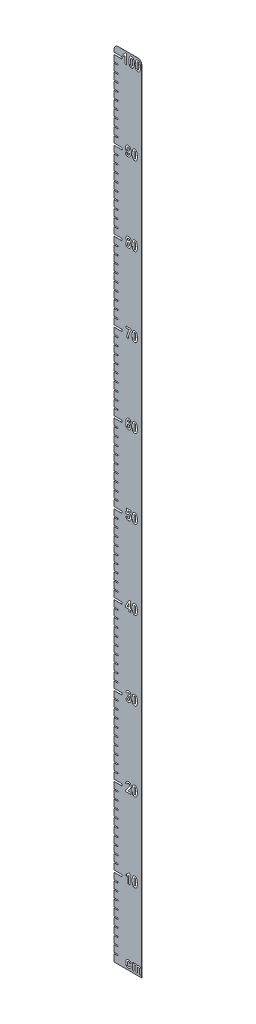
SolidWorks part; units mm, degrees
ref_plane "Plano frontal" through (0, 0, 0) normal (0, 0, 1) x (1, 0, 0)
ref_plane "Plano superior" through (0, 0, 0) normal (0, 1, 0) x (1, 0, 0)
ref_plane "Plano direito" through (0, 0, 0) normal (1, 0, 0) x (0, 0, -1)
sketch "Esboço1" plane through (0, 0, 0) normal (0, 0, 1) x (1, 0, 0)
  line L1 (0, 0) -> (35, 0)
  line L2 (0, 0) -> (0, 1010)
  line L3 (0, 1010) -> (35, 1010)
  line L4 (35, 0) -> (35, 1010)
  dimension "D1" = 1010
  dimension "D2" = 35
extrude "Ressalto-extrusão1" add sketch "Esboço1" along normal blind 0.1
sketch "Esboço2" plane through (0, 0, 0.1) normal (0, 0, 1) x (1, 0, 0)
  line L0 (0, 10) -> (5, 10)
  line L1 (0, 1010) -> (0, 0) construction
  line L2 (0, 0) -> (35, 0) construction
  dimension "D1" = 5
  dimension "D2" = 10
extrude "Corte-Extrusão-Fina1" cut sketch "Esboço2" against normal blind 1 and the other way through all thin thin type mid plane wall 1.5
pattern_linear "Padrão linear1" count 9 spacing 10 along (0, 1, 0) of "Corte-Extrusão-Fina1"
sketch "Esboço3" plane through (0, 0, 0.1) normal (0, 0, 1) x (1, 0, 0)
  line L0 (0, 100) -> (10, 100)
  line L1 (0, 1010) -> (0, 90.75) construction
  line L2 (0, 0) -> (35, 0) construction
  dimension "D1" = 10
  dimension "D2" = 100
extrude "Corte-Extrusão-Fina2" cut sketch "Esboço3" against normal blind 1 and the other way through all thin thin type mid plane wall 2.5
pattern_linear "Padrão linear2" count 2 spacing 100 along (0, 1, 0) of "Corte-Extrusão-Fina2"
pattern_linear "Padrão linear3" count 10 spacing 100 along (0, 1, 0) of "Corte-Extrusão-Fina1", "Padrão linear1", "Corte-Extrusão-Fina2"
sketch "Esboço5" plane through (0, 0, 0.1) normal (0, 0, 1) x (1, 0, 0)
  line L0 (10, 95) -> (40, 95) construction
  line L2 (10, 101.25) -> (10, 98.75) construction
  line L3 (10, 195.011) -> (40, 195.011) construction
  line L4 (10, 295.022) -> (40, 295.022) construction
  line L5 (10, 395.0329) -> (40, 395.0329) construction
  line L6 (10, 495.0439) -> (40, 495.0439) construction
  line L7 (10, 595.0549) -> (40, 595.0549) construction
  line L8 (10, 695.0659) -> (40, 695.0659) construction
  line L9 (10, 795.0768) -> (40, 795.0768) construction
  line L10 (10, 895.0878) -> (40, 895.0878) construction
  line L11 (10, 995.0988) -> (40, 995.0988) construction
  line L17 (35, 0) -> (35, 1010) construction
  line L18 (35, 1.5) -> (15, 1.5) construction
  line L19 (0, 0) -> (35, 0) construction
  line L20 (10, 1495.1537) -> (40, 1495.1537) construction
  line L21 (10, 1395.1427) -> (40, 1395.1427) construction
  line L22 (10, 1295.1317) -> (40, 1295.1317) construction
  line L23 (10, 1195.1207) -> (40, 1195.1207) construction
  line L24 (10, 1095.1098) -> (40, 1095.1098) construction
  text T0 " 10"
  text T1 " 20"
  text T2 " 30"
  text T3 " 40"
  text T4 " 50"
  text T5 " 60"
  text T6 " 70"
  text T7 " 80\r\n"
  text T8 " 90\r\n"
  text T10 "100\r\n"
  text T12 "   cm"
  point P5 (10, 100)
  point P26 (25, 998.0988)
  point P27 (0, 0)
  dimension "D1" = 30
  dimension "D2" = 5
  dimension "D4" = 20
  dimension "D5" = 1.5
  dimension "D3" = 15
extrude "Corte-extrusão1" cut sketch "Esboço5" against normal blind 1
fillet "Filete1" radius 5 2 edges at (0, 1010, 0.05) (35, 1010, 0.05)
